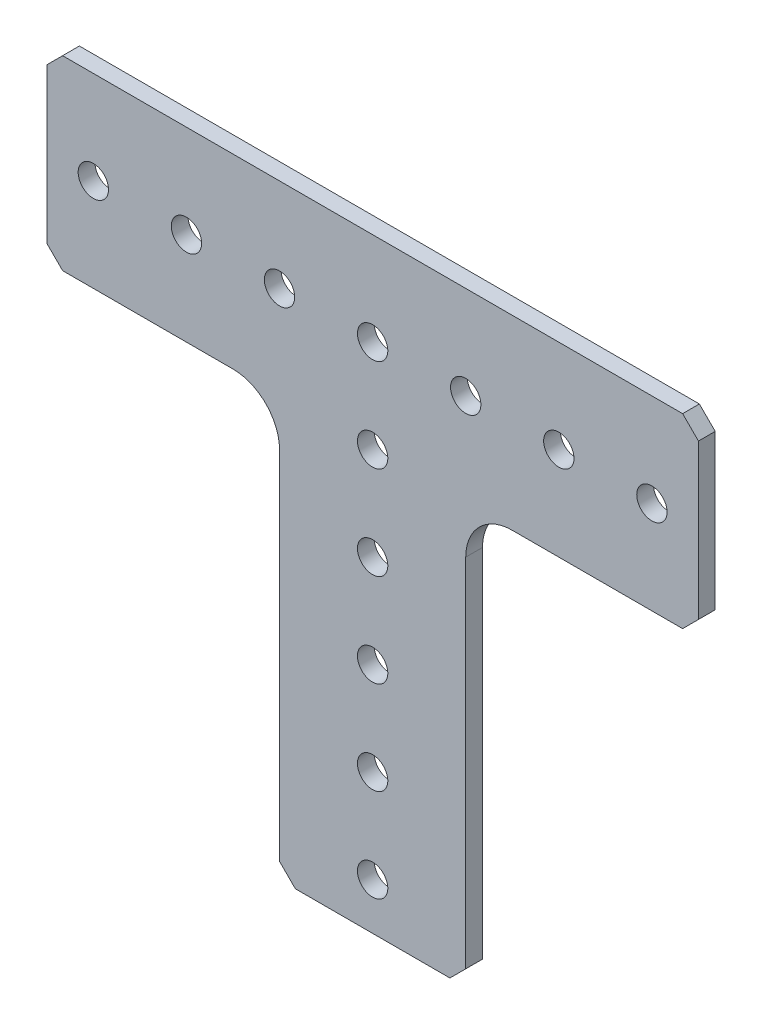
SolidWorks part; units mm, degrees
ref_plane "Front Plane" through (0, 0, 0) normal (0, 0, 1) x (1, 0, 0)
ref_plane "Top Plane" through (0, 0, 0) normal (0, 1, 0) x (1, 0, 0)
ref_plane "Right Plane" through (0, 0, 0) normal (1, 0, 0) x (0, 0, -1)
ref_plane "Plane1" through (0, 0, 2.286) normal (0, 0, 1) x (1, 0, 0)
sketch "Sketch1" plane through (0, 0, 2.286) normal (0, 0, 1) x (1, 0, 0)
  line L0 (12.7, -54.991) -> (12.7, -6.35)
  line L1 (19.05, 0) -> (42.291, 0)
  line L2 (42.291, 0) -> (44.45, 2.159)
  line L3 (44.45, 2.159) -> (44.45, 23.241)
  line L4 (44.45, 23.241) -> (42.291, 25.4)
  line L5 (42.291, 25.4) -> (-42.291, 25.4)
  line L6 (-42.291, 25.4) -> (-44.45, 23.241)
  line L7 (-44.45, 23.241) -> (-44.45, 2.159)
  line L8 (-44.45, 2.159) -> (-42.291, 0)
  line L9 (-42.291, 0) -> (-19.05, 0)
  line L10 (-12.7, -6.35) -> (-12.7, -54.991)
  line L11 (-12.7, -54.991) -> (-10.541, -57.15)
  line L12 (-10.541, -57.15) -> (10.541, -57.15)
  line L13 (10.541, -57.15) -> (12.7, -54.991)
  circle A0 centre (0, -38.1) radius 2.0701
  circle A1 centre (0, -12.7) radius 2.0701
  circle A2 centre (38.1, 12.7) radius 2.0701
  circle A3 centre (12.7, 12.7) radius 2.0701
  circle A4 centre (-12.7, 12.7) radius 2.0701
  circle A5 centre (-38.1, 12.7) radius 2.0701
  circle A6 centre (-25.4, 12.7) radius 2.0701
  circle A7 centre (0, 12.7) radius 2.0701
  circle A8 centre (25.4, 12.7) radius 2.0701
  circle A9 centre (0, 0) radius 2.0701
  circle A10 centre (0, -25.4) radius 2.0701
  circle A11 centre (0, -50.8) radius 2.0701
  arc A12 (12.7, -6.35) -> (19.05, 0) centre (19.05, -6.35) cw
  arc A13 (-19.05, 0) -> (-12.7, -6.35) centre (-19.05, -6.35) cw
  dimension "D1" = 4.1402
  dimension "D2" = 4.1402
extrude "Boss-Extrude1" add sketch "Sketch1" against normal blind 2.286
